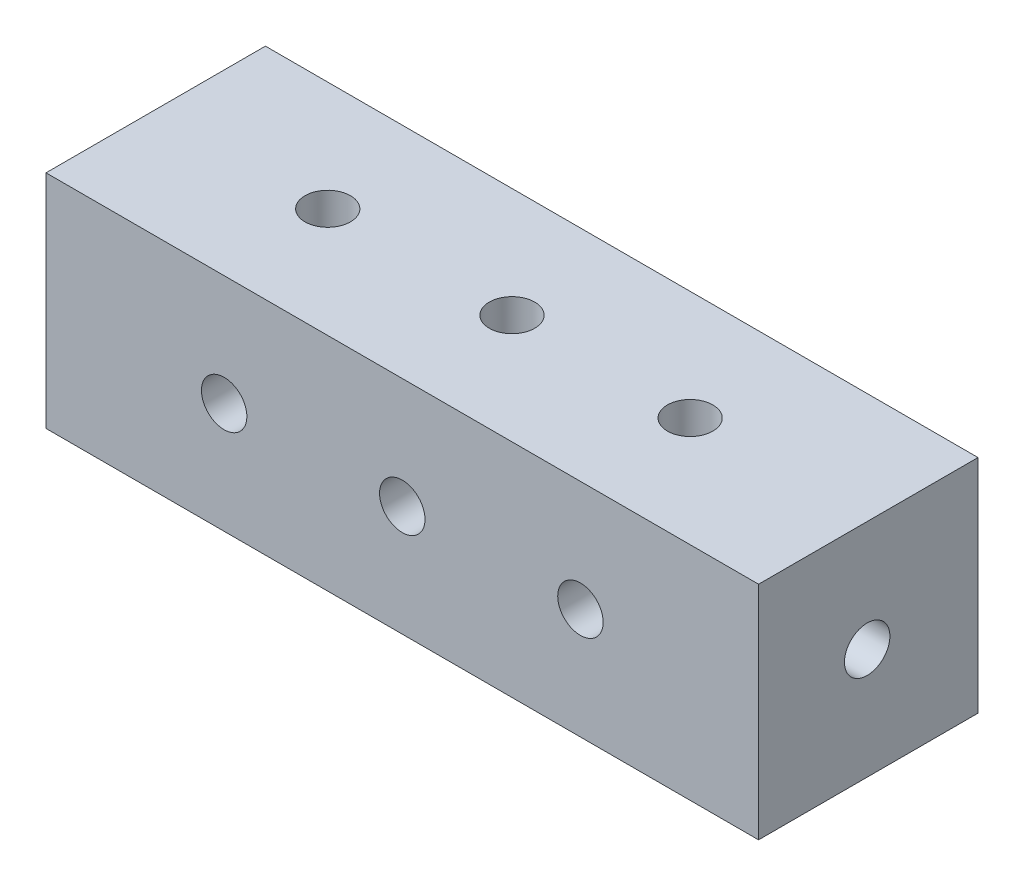
SolidWorks part; units mm, degrees
ref_plane "Plano frontal" through (0, 0, 0) normal (0, 0, 1) x (1, 0, 0)
ref_plane "Plano superior" through (0, 0, 0) normal (0, 1, 0) x (1, 0, 0)
ref_plane "Plano direito" through (0, 0, 0) normal (1, 0, 0) x (0, 0, -1)
sketch "Esboço1" plane through (0, 0, 0) normal (0, 0, 1) x (1, 0, 0)
  line L1 (0, 0) -> (128.6, 0)
  line L2 (0, 0) -> (0, 39.96)
  line L3 (0, 39.96) -> (128.6, 39.96)
  line L4 (128.6, 0) -> (128.6, 39.96)
  dimension "D1" = 128.6
  dimension "D2" = 39.96
extrude "Ressalto-extrusão1" add sketch "Esboço1" along normal blind 39.6
sketch "Esboço2" plane through (0, 0, 0) normal (0, 1, 0) x (1, 0, 0)
  line L0 (0, -19.8) -> (128.6, -19.8) construction
  line L1 (0, -39.6) -> (0, 0) construction
  line L2 (128.6, -39.6) -> (128.6, 0) construction
  line L3 (128.6, -19.8) -> (64.3, 0) construction
  line L4 (128.6, 0) -> (0, 0) construction
  line L5 (64.3, 0) -> (64.3, -39.6) construction
  line L6 (128.6, -39.6) -> (0, -39.6) construction
  line L7 (64.3, -39.6) -> (0, 0) construction
  line L8 (0, 0) -> (0, -39.6) construction
  line L9 (0, -39.6) -> (64.3, 0) construction
  line L10 (64.3, 0) -> (64.3, -39.6) construction
  line L11 (64.3, -39.6) -> (128.6, 0) construction
  line L12 (128.6, 0) -> (128.6, -39.6) construction
  line L13 (128.6, -39.6) -> (64.3, 0) construction
  circle A0 centre (31.0445, -19.8) radius 4.1
  circle A1 centre (96.45, -19.8) radius 4.1
  circle A2 centre (64.3, -19.8) radius 4.1
  dimension "D1" = 8.2
  dimension "D2" = 8.2
  dimension "D3" = 8.2
extrude "Corte-extrusão1" cut sketch "Esboço2" along direction (0, -1, 0) on the side of the normal blind 49 and the other way blind 9
sketch "Esboço3" plane through (0, 0, 0) normal (1, 0, 0) x (0, 0, -1)
  line L1 (0, 0) -> (-39.6, 0) construction
  circle A0 centre (-20, 20) radius 4.1
  dimension "7.8" = 8.2
extrude "Corte-extrusão2" cut sketch "Esboço3" along direction (-1, 0, 0) on the side of the normal blind 157 and the other way blind 19
sketch "Esboço4" plane through (0, 0, 0) normal (0, 0, 1) x (1, 0, 0)
  line L0 (0, 39.96) -> (128.6, 0) construction
  line L1 (128.6, 0) -> (128.6, 39.96) construction
  line L2 (128.6, 39.96) -> (0, 0) construction
  line L3 (0, 0) -> (64.3, 0) construction
  line L4 (0, 0) -> (128.6, 0) construction
  line L5 (64.3, 0) -> (64.3, 39.96) construction
  line L6 (128.6, 39.96) -> (0, 39.96) construction
  line L7 (64.3, 39.96) -> (128.6, 0) construction
  line L8 (128.6, 0) -> (128.6, 39.96) construction
  line L9 (128.6, 39.96) -> (64.3, 0) construction
  line L10 (64.3, 0) -> (0, 39.96) construction
  line L11 (0, 39.96) -> (0, 0) construction
  line L12 (0, 0) -> (64.3, 39.96) construction
  circle A0 centre (32.15, 19.98) radius 4.1
  circle A1 centre (64.3, 19.98) radius 4.1
  circle A2 centre (96.45, 19.98) radius 4.1
  dimension "D1" = 8.2
  dimension "D2" = 8.2
  dimension "D3" = 8.2
extrude "Corte-extrusão3" cut sketch "Esboço4" along direction (0, 0, -1) on the side of the normal blind 64 and the other way blind 26
